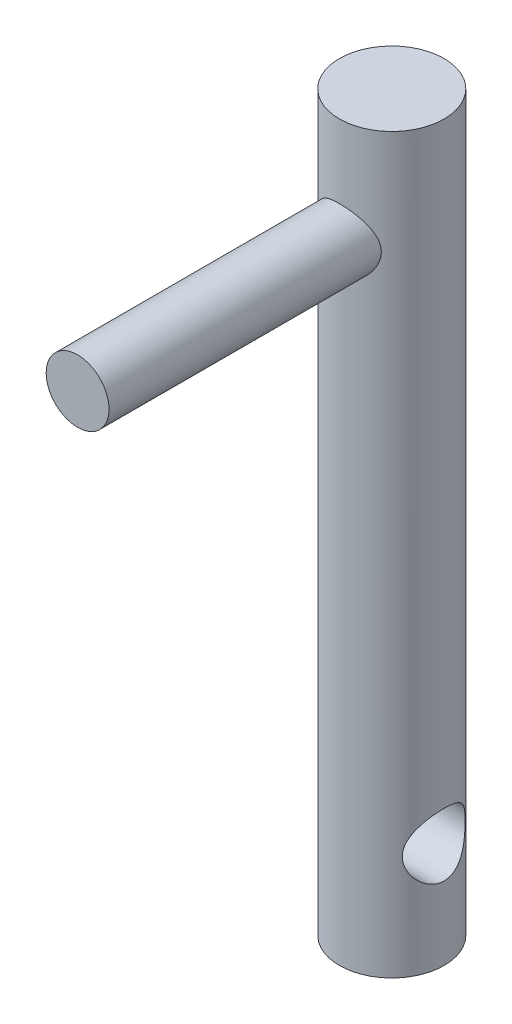
SolidWorks part; units mm, degrees
ref_plane "Front Plane" through (0, 0, 0) normal (0, 0, 1) x (1, 0, 0)
ref_plane "Top Plane" through (0, 0, 0) normal (0, 1, 0) x (1, 0, 0)
ref_plane "Right Plane" through (0, 0, 0) normal (1, 0, 0) x (0, 0, -1)
sketch "Sketch1" plane through (0, 0, 0) normal (0, 1, 0) x (1, 0, 0)
  circle A0 centre (0, 0) radius 2.5
  dimension "D1" = 5
extrude "Boss-Extrude1" add sketch "Sketch1" along normal blind 35
sketch "Sketch2" plane through (0, 0, 0) normal (1, 0, 0) x (0, 0, -1)
  circle A0 centre (0, 5) radius 1.5
  dimension "D1" = 3
  dimension "D2" = 5
extrude "Cut-Extrude1" cut sketch "Sketch2" against normal through all both and the other way through all
sketch "Sketch4" plane through (0, 0, 0) normal (0, 0, 1) x (1, 0, 0)
  line L0 (2.5, 35) -> (-2.5, 35) construction
  line L1 (0, 30) -> (0, 35) construction
  circle A0 centre (0, 30) radius 1.5
  dimension "D1" = 3
  dimension "D2" = 5
extrude "Boss-Extrude3" add sketch "Sketch4" along normal blind 15
